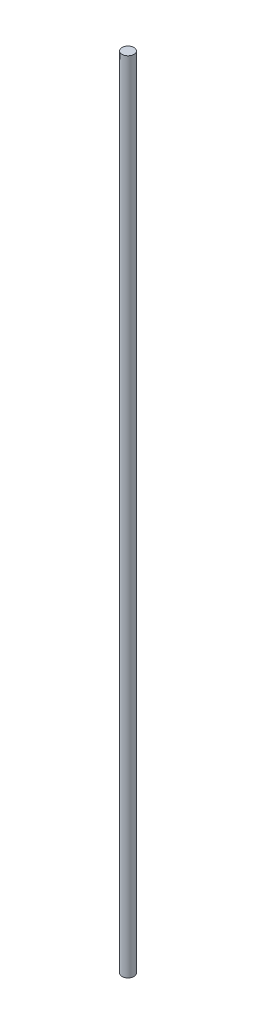
SolidWorks part; units mm, degrees
material "AISI Type A2 Tool Steel"
ref_plane "Front Plane" through (0, 0, 0) normal (0, 0, 1) x (1, 0, 0)
ref_plane "Top Plane" through (0, 0, 0) normal (0, 1, 0) x (1, 0, 0)
ref_plane "Right Plane" through (0, 0, 0) normal (1, 0, 0) x (0, 0, -1)
sketch "Sketch1" plane through (0, 0, 0) normal (0, 1, 0) x (1, 0, 0)
  circle A0 centre (0, 0) radius 1.5
  dimension "D1" = 3
extrude "Boss-Extrude1" add sketch "Sketch1" along normal blind 200
